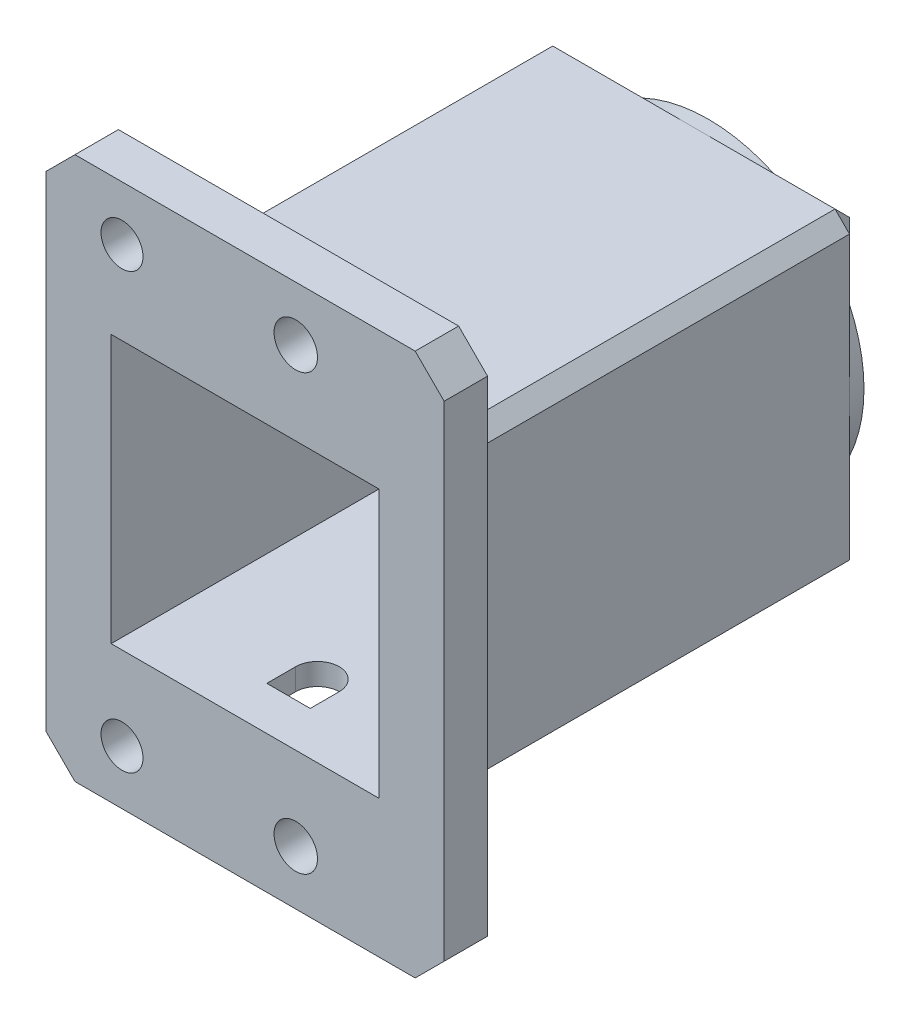
SolidWorks part; units mm, degrees
ref_plane "Front Plane" through (0, 0, 0) normal (0, 0, 1) x (1, 0, 0)
ref_plane "Top Plane" through (0, 0, 0) normal (0, 1, 0) x (1, 0, 0)
ref_plane "Right Plane" through (0, 0, 0) normal (1, 0, 0) x (0, 0, -1)
sketch "Sketch1" plane through (0, 0, 0) normal (0, 0, 1) x (1, 0, 0)
  line L0 (-10.75, 10.75) -> (10.75, 10.75)
  line L1 (-9.25, -9.25) -> (9.25, -9.25) construction
  line L2 (-9.25, -9.25) -> (-9.25, 9.25) construction
  line L3 (-9.25, 9.25) -> (9.25, 9.25) construction
  line L4 (9.25, -9.25) -> (9.25, 9.25) construction
  line L5 (-9.25, -9.25) -> (9.25, 9.25) construction
  line L6 (-9.25, 9.25) -> (9.25, -9.25) construction
  line L7 (10.75, -10.75) -> (10.75, 10.75)
  line L8 (-10.75, -10.75) -> (10.75, -10.75)
  line L9 (-10.75, -10.75) -> (-10.75, 10.75)
  circle A0 centre (0, 0) radius 8 construction
  circle A1 centre (0, 0) radius 8
  circle A2 centre (0, 0) radius 10.75 construction
  circle A3 centre (0, 0) radius 10.75 construction
  dimension "D1" = 18.5
  dimension "D2" = 1.5
extrude "Boss-Extrude1" add sketch "Sketch1" along normal blind 2
sketch "Sketch2" plane through (0, 0, 2) normal (0, 0, 1) x (1, 0, 0)
  line L0 (9.25, -9.25) -> (9.25, 9.25)
  line L1 (9.25, 9.25) -> (-9.25, 9.25)
  line L2 (-9.25, 9.25) -> (-9.25, -9.25)
  line L3 (-9.25, -9.25) -> (9.25, -9.25)
  line L4 (-10.75, 10.75) -> (-10.75, -10.75)
  line L5 (-10.75, -10.75) -> (10.75, -10.75)
  line L6 (10.75, -10.75) -> (10.75, 10.75)
  line L7 (10.75, 10.75) -> (-10.75, 10.75)
  line L8 (-10.75, 10.75) -> (-10.75, -10.75)
  line L9 (-10.75, -10.75) -> (10.75, -10.75)
  line L10 (10.75, -10.75) -> (10.75, 10.75)
  line L11 (10.75, 10.75) -> (-10.75, 10.75)
  dimension "D1" = 0
  dimension "D2" = 1.5
extrude "Boss-Extrude2" add sketch "Sketch2" along normal up to surface (30 mm away)
sketch "Sketch3" plane through (0, 0, 32) normal (0, 0, 1) x (1, 0, 0)
  line L0 (-8.5, 15) -> (-8.5, -15) construction
  line L3 (-13.75, -18.75) -> (13.75, -18.75)
  line L4 (-13.75, -18.75) -> (-13.75, 18.75)
  line L5 (-13.75, 18.75) -> (13.75, 18.75)
  line L6 (-10.75, 10.75) -> (-10.75, -10.75)
  line L7 (-10.75, -10.75) -> (10.75, -10.75)
  line L8 (10.75, -10.75) -> (10.75, 10.75)
  line L9 (10.75, 10.75) -> (-10.75, 10.75)
  line L10 (-10.75, 10.75) -> (-10.75, -10.75)
  line L11 (-10.75, -10.75) -> (10.75, -10.75)
  line L12 (10.75, -10.75) -> (10.75, 10.75)
  line L13 (10.75, 10.75) -> (-10.75, 10.75)
  line L14 (13.75, -18.75) -> (13.75, 18.75)
  line L15 (-13.75, -18.75) -> (13.75, 18.75) construction
  line L16 (-13.75, 18.75) -> (13.75, -18.75) construction
  circle A0 centre (3.5, -15) radius 1.5 construction
  circle A1 centre (3.5, -15) radius 1.5
  circle A2 centre (3.5, 15) radius 1.5 construction
  circle A3 centre (3.5, 15) radius 1.5
  circle A4 centre (-8.5, 15) radius 1.5 construction
  circle A5 centre (-8.5, 15) radius 1.5
  circle A6 centre (-8.5, -15) radius 1.5 construction
  circle A7 centre (-8.5, -15) radius 1.5
  point P12 (0, 0)
  dimension "D1" = 0
  dimension "D2" = 8
  dimension "D3" = 3
extrude "Boss-Extrude3" add sketch "Sketch3" against normal blind 3
sketch "Sketch4" plane through (0, -10.75, 0) normal (0, -1, 0) x (1, 0, 0)
  line L0 (0, 0) -> (0, 29) construction
  line L1 (-13.75, 29) -> (13.75, 29) construction
  line L2 (1.5, 27) -> (1.5, 29)
  line L3 (1.5, 29) -> (-1.5, 29)
  line L4 (-1.5, 29) -> (-1.5, 27)
  circle A0 centre (0, 27) radius 1.5
  line M3 (10.75, 29) -> (-10.75, 29)
  dimension "D1" = 3
  dimension "D2" = 2
extrude "Cut-Extrude1" cut sketch "Sketch4" against normal blind 3 contours A0 L0 | L0 A0 | L0 A0 L2 M3 | A0 L0 L3 L4
chamfer "Chamfer1" distance 1 angle 45 8 edges at (10.75, -10.75, 14.5) (0, -10.75, 0) (-10.75, -10.75, 14.5) (-10.75, 0, 0) (-10.75, 10.75, 14.5) (0, 10.75, 0) (10.75, 10.75, 14.5) (10.75, 0, 0)
chamfer "Chamfer2" distance 2 angle 45 4 edges at (-13.75, 18.75, 30.5) (-13.75, -18.75, 30.5) (13.75, 18.75, 30.5) (13.75, -18.75, 30.5)
sketch "Sketch5" plane through (0, 0, 29) normal (0, 0, -1) x (-1, 0, 0)
  circle A0 centre (8.5, -15) radius 1.5 construction
  circle A1 centre (8.5, -15) radius 1.5
  circle A2 centre (8.5, 15) radius 1.5 construction
  circle A3 centre (8.5, 15) radius 1.5
  circle A4 centre (8.5, 15) radius 1.45
  circle A5 centre (8.5, -15) radius 1.45
  dimension "D1" = 2.9
  dimension "D2" = 2.9
extrude "Boss-Extrude4" add sketch "Sketch5" against normal up to surface (3 mm away) up to face at (0, 0, 32)
sketch "Sketch6" plane through (0, 0, 0) normal (0, 0, -1) x (-1, 0, 0)
  line L0 (-10.75, -9.75) -> (-10.75, 9.75) construction
  circle A0 centre (0, 0) radius 10.75
  circle A1 centre (0, 0) radius 8 construction
  circle A2 centre (0, 0) radius 8
extrude "Boss-Extrude5" add sketch "Sketch6" against normal blind 1.5
sketch "Sketch7" plane through (0, 0, 2) normal (0, 0, 1) x (1, 0, 0)
  circle A0 centre (0, 0) radius 8 construction
  circle A1 centre (0, 0) radius 8
extrude "Boss-Extrude6" [suppressed] add sketch "Sketch7" against normal blind 0.2
